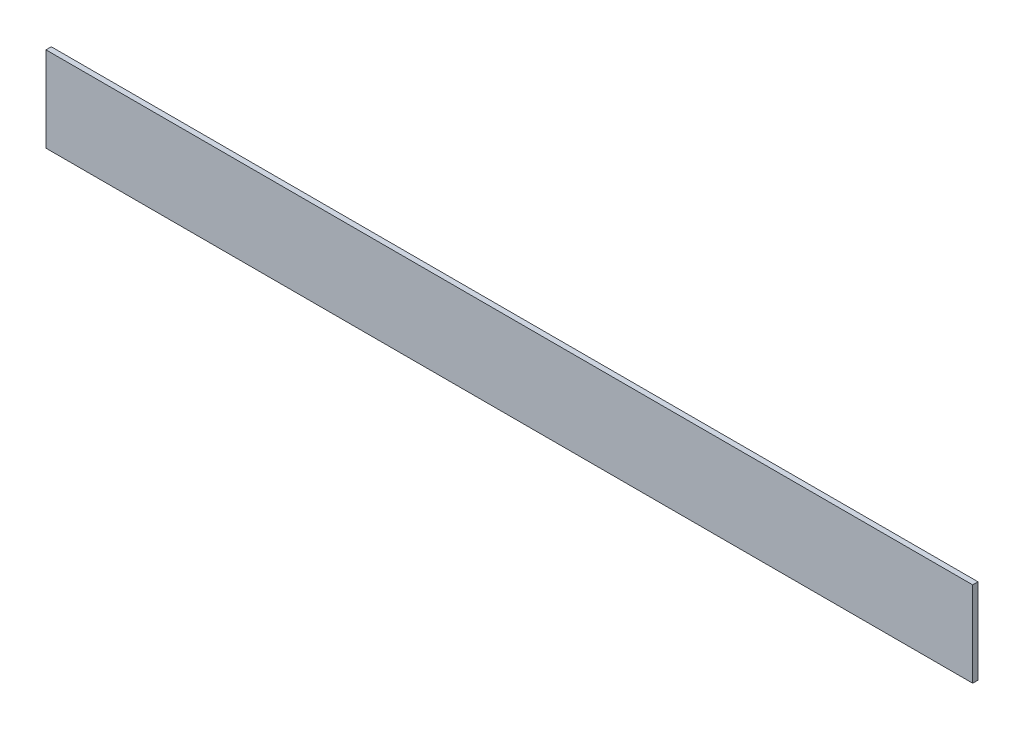
SolidWorks part; units mm, degrees
ref_plane "Front Plane" through (0, 0, 0) normal (0, 0, 1) x (1, 0, 0)
ref_plane "Top Plane" through (0, 0, 0) normal (0, 1, 0) x (1, 0, 0)
ref_plane "Right Plane" through (0, 0, 0) normal (1, 0, 0) x (0, 0, -1)
sketch "Sketch1" plane through (0, 0, 0) normal (0, 0, 1) x (1, 0, 0)
  line L1 (0, 0) -> (552.45, 0)
  line L2 (0, 0) -> (0, 50.8)
  line L3 (0, 50.8) -> (552.45, 50.8)
  line L4 (552.45, 0) -> (552.45, 50.8)
  dimension "D1" = 50.8
  dimension "D2" = 552.45
extrude "Boss-Extrude1" add sketch "Sketch1" along normal blind 3.175
